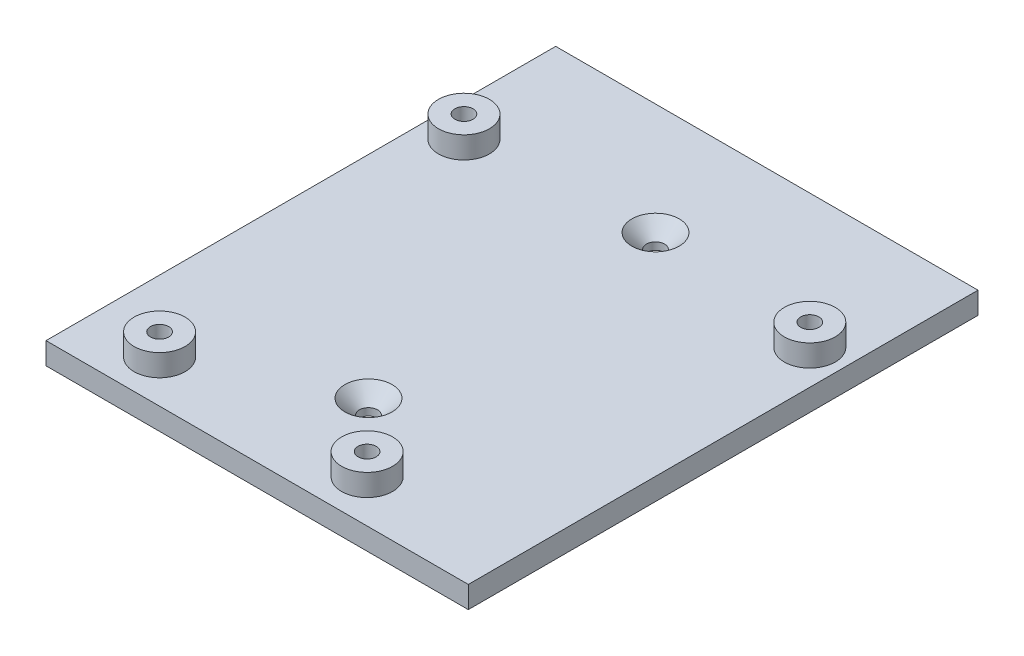
SolidWorks part; units mm, degrees
ref_plane "Спереди" through (0, 0, 0) normal (0, 0, 1) x (1, 0, 0)
ref_plane "Сверху" through (0, 0, 0) normal (0, 1, 0) x (1, 0, 0)
ref_plane "Справа" through (0, 0, 0) normal (1, 0, 0) x (0, 0, -1)
other "Configuration Table"
sketch "Эскиз1" plane through (0, 0, 0) normal (0, 1, 0) x (1, 0, 0)
  line L0 (-22.6919, 10.6033) -> (30.8081, 10.6033) construction
  line L1 (-24.9419, 13.9533) -> (33.0581, 13.9533)
  line L2 (-24.9419, 13.9533) -> (-24.9419, -56.0467)
  line L3 (-24.9419, -56.0467) -> (33.0581, -56.0467)
  line L4 (33.0581, 13.9533) -> (33.0581, -56.0467)
  line L5 (30.8081, 10.6033) -> (30.8081, -52.6967) construction
  line L6 (30.8081, -52.6967) -> (-22.6919, -52.6967) construction
  line L7 (-22.6919, -52.6967) -> (-22.6919, 10.6033) construction
  line L8 (-24.9419, -21.0467) -> (33.0581, -21.0467) construction
  line L9 (-22.6919, -21.0467) -> (30.8081, -21.0467)
  line L10 (4.0581, 13.9533) -> (4.0581, -56.0467) construction
  line L11 (4.0581, -52.6967) -> (4.0581, 10.6033) construction
  dimension "D4" = 63.3
  dimension "D1" = 58
  dimension "D2" = 70
  dimension "D3" = 53.5
extrude "Бобышка-Вытянуть1" add sketch "Эскиз1" along normal blind 3 contours L1 L4 L3 L2
sketch "Эскиз2" plane through (0, 3, 0) normal (0, 1, 0) x (1, 0, 0)
  line L0 (-22.6919, 10.6033) -> (30.8081, 10.6033) construction
  line L1 (30.8081, 10.6033) -> (30.8081, -52.6967) construction
  line L2 (30.8081, -52.6967) -> (-22.6919, -52.6967) construction
  line L3 (-22.6919, -52.6967) -> (-22.6919, 10.6033) construction
  line L4 (-24.4419, -21.0467) -> (32.5581, -21.0467) construction
  line L5 (-22.6919, -21.0467) -> (30.8081, -21.0467) construction
  line L6 (4.0581, 13.855) -> (4.0581, -56.145) construction
  line L7 (4.0581, -52.6967) -> (4.0581, 10.6033) construction
  line L8 (4.0581, 13.9533) -> (4.0581, -56.0467) construction
  line L9 (-24.9419, 13.9533) -> (33.0581, 13.9533) construction
  line L10 (-24.9419, -56.0467) -> (33.0581, -56.0467) construction
  line L11 (-24.9419, -21.0467) -> (33.0581, -21.0467) construction
  line L12 (-24.9419, 13.9533) -> (-24.9419, -56.0467) construction
  line L13 (33.0581, 13.9533) -> (33.0581, -56.0467) construction
  circle A0 centre (28.3081, -4.3967) radius 3.5
  circle A1 centre (28.3081, -4.3967) radius 1.25
  circle A2 centre (-20.1919, -3.3967) radius 3.5
  circle A3 centre (-20.1919, -3.3967) radius 1.25
  circle A4 centre (-15.1919, -50.1967) radius 3.5
  circle A5 centre (-15.1919, -50.1967) radius 1.25
  circle A6 centre (13.3081, -50.1967) radius 3.5
  circle A7 centre (13.3081, -50.1967) radius 1.25
  point P29 (-21.2388, -4.0168)
  point P33 (-20.7438, -4.7239)
  point P35 (-15.916, -48.1593)
  point P36 (0, 0)
  point P40 (24.0088, -48.9789)
  point P43 (17.983, -51.7076)
  point P44 (14.6168, -49.8429)
  dimension "D3" = 15
  dimension "D5" = 7
  dimension "D6" = 2.5
  dimension "D8" = 7
  dimension "D9" = 2.5
  dimension "D1" = 53.5
  dimension "D2" = 63.3
  dimension "D4" = 2.5
  dimension "D7" = 14
  dimension "D10" = 2.5
  dimension "D11" = 7.5
  dimension "D12" = 2.5
  dimension "D13" = 17.5
  dimension "D14" = 2.5
extrude "Бобышка-Вытянуть2" add sketch "Эскиз2" along normal blind 3
sketch "Эскиз3" plane through (0, 3, 0) normal (0, 1, 0) x (1, 0, 0)
  line L0 (4.0581, 13.9533) -> (4.0581, -56.0467) construction
  line L1 (-24.9419, 13.9533) -> (33.0581, 13.9533) construction
  line L2 (-24.9419, -56.0467) -> (33.0581, -56.0467) construction
  line L4 (-24.9419, -21.0467) -> (33.0581, -21.0467) construction
  line L5 (-24.9419, 13.9533) -> (-24.9419, -56.0467) construction
  line L6 (33.0581, 13.9533) -> (33.0581, -56.0467) construction
  circle A0 centre (4.0581, -1.3351) radius 1.25
  circle A1 centre (4.0581, -40.7582) radius 1.25
  point P16 (4.0581, -1.3351)
extrude "Вырез-Вытянуть1" cut sketch "Эскиз3" against normal blind 3
chamfer "Фаска1" distance 2 angle 45 2 edges at (4.0581, 3, 39.5082) (4.0581, 3, 2.5851)
